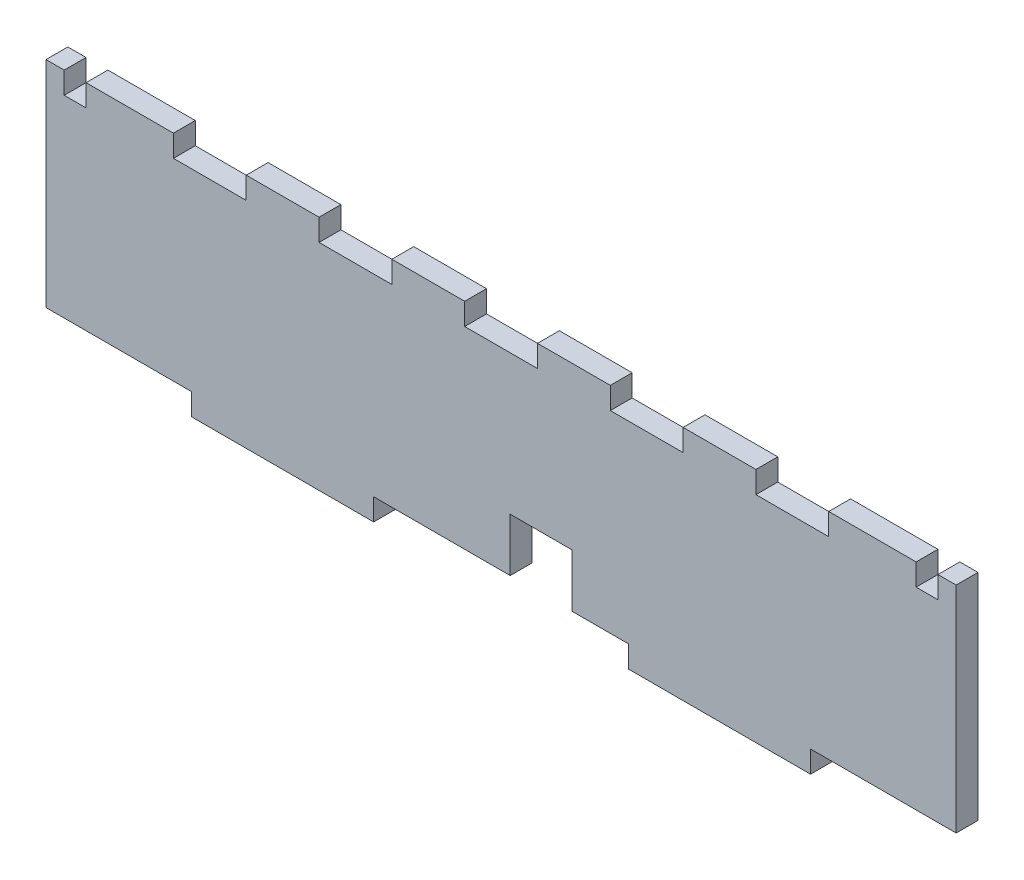
SolidWorks part; units mm, degrees
ref_plane "Front Plane" through (0, 0, 0) normal (0, 0, 1) x (1, 0, 0)
ref_plane "Top Plane" through (0, 0, 0) normal (0, 1, 0) x (1, 0, 0)
ref_plane "Right Plane" through (0, 0, 0) normal (1, 0, 0) x (0, 0, -1)
sketch "Sketch1" plane through (0, 0, 0) normal (0, 0, 1) x (1, 0, 0)
  line L1 (-125, -32.5) -> (125, -32.5)
  line L2 (-125, -32.5) -> (-125, 32.5)
  line L3 (-125, 32.5) -> (125, 32.5)
  line L4 (125, -32.5) -> (125, 32.5)
  line L5 (-125, -32.5) -> (125, 32.5) construction
  line L6 (-125, 32.5) -> (125, -32.5) construction
  line L7 (-125, -32.5) -> (-85, -32.5)
  line L8 (-125, -32.5) -> (-125, -26.5)
  line L9 (-125, -26.5) -> (-85, -26.5)
  line L10 (-85, -32.5) -> (-85, -26.5)
  line L11 (125, -32.5) -> (85, -32.5)
  line L12 (125, -32.5) -> (125, -26.5)
  line L13 (125, -26.5) -> (85, -26.5)
  line L14 (85, -32.5) -> (85, -26.5)
  line L15 (-35, -32.5) -> (35, -32.5)
  line L16 (-35, -32.5) -> (-35, -26.5)
  line L17 (-35, -26.5) -> (35, -26.5)
  line L18 (35, -32.5) -> (35, -26.5)
  point P0 (0, 0)
  point P16 (0, -26.5)
  point P17 (0, -32.5)
  dimension "D1" = 6
  dimension "D2" = 6
  dimension "D3" = 6
  dimension "D4" = 40
  dimension "D5" = 40
  dimension "D6" = 250
  dimension "D7" = 70
  dimension "D8" = 65
extrude "Boss-Extrude1" add sketch "Sketch1" along normal blind 6
sketch "Sketch2" plane through (0, 0, 6) normal (0, 0, 1) x (1, 0, 0)
  line L0 (-125, 32.5) -> (125, 32.5) construction
  line L1 (-90, 32.5) -> (-70, 32.5)
  line L2 (-90, 32.5) -> (-90, 26.5)
  line L3 (-90, 26.5) -> (-70, 26.5)
  line L4 (-70, 32.5) -> (-70, 26.5)
  line L5 (-50, 26.5) -> (-30, 26.5)
  line L6 (-30, 32.5) -> (-30, 26.5)
  line L7 (-50, 32.5) -> (-30, 32.5)
  line L8 (-50, 32.5) -> (-50, 26.5)
  line L9 (-10, 26.5) -> (10, 26.5)
  line L10 (10, 32.5) -> (10, 26.5)
  line L11 (-10, 32.5) -> (10, 32.5)
  line L12 (-10, 32.5) -> (-10, 26.5)
  line L13 (30, 26.5) -> (50, 26.5)
  line L14 (50, 32.5) -> (50, 26.5)
  line L15 (30, 32.5) -> (50, 32.5)
  line L16 (30, 32.5) -> (30, 26.5)
  line L17 (70, 26.5) -> (90, 26.5)
  line L18 (90, 32.5) -> (90, 26.5)
  line L19 (70, 32.5) -> (90, 32.5)
  line L20 (70, 32.5) -> (70, 26.5)
  line L22 (-120, 32.5) -> (-114, 32.5)
  line L23 (-120, 32.5) -> (-120, 26.5)
  line L24 (-120, 26.5) -> (-114, 26.5)
  line L25 (-114, 32.5) -> (-114, 26.5)
  line L26 (114, 32.5) -> (120, 32.5)
  line L27 (114, 32.5) -> (114, 26.5)
  line L28 (114, 26.5) -> (120, 26.5)
  line L29 (120, 32.5) -> (120, 26.5)
  dimension "D1" = 6
  dimension "D2" = 35
  dimension "D3" = 20
  dimension "D5" = 5
  dimension "D6" = 5
  dimension "D7" = 6
  dimension "D8" = 6
  dimension "D4" = 5
extrude "Cut-Extrude1" cut sketch "Sketch2" against normal up to next
sketch "Sketch3" plane through (0, 0, 0) normal (0, 0, -1) x (-1, 0, 0)
  line L0 (-19.507, -11.9) -> (-19.507, -27.4)
  line L1 (-16.507, -14.9) -> (-5.507, -14.9) construction
  line L2 (-16.507, -14.9) -> (-16.507, -24.4) construction
  line L3 (-16.507, -24.4) -> (-5.507, -24.4) construction
  line L4 (-5.507, -14.9) -> (-5.507, -24.4) construction
  line L5 (-19.507, -27.4) -> (-2.507, -27.4)
  line L6 (-2.507, -11.9) -> (-2.507, -27.4)
  line L7 (-19.507, -11.9) -> (-2.507, -11.9)
  dimension "D1" = 3
extrude "Cut-Extrude2" cut sketch "Sketch3" against normal up to next
equation "\"Material Thickness\"= 6"
equation "\"D1@Sketch1\"=\"Material Thickness\""
equation "\"D2@Sketch1\"=\"Material Thickness\""
equation "\"D3@Sketch1\"=\"Material Thickness\""
equation "\"D1@Boss-Extrude1\"=\"Material Thickness\""
equation "\"D1@Sketch2\"=\"Material Thickness\""
equation "\"D7@Sketch2\"=\"Material Thickness\""
equation "\"D8@Sketch2\"=\"Material Thickness\""
